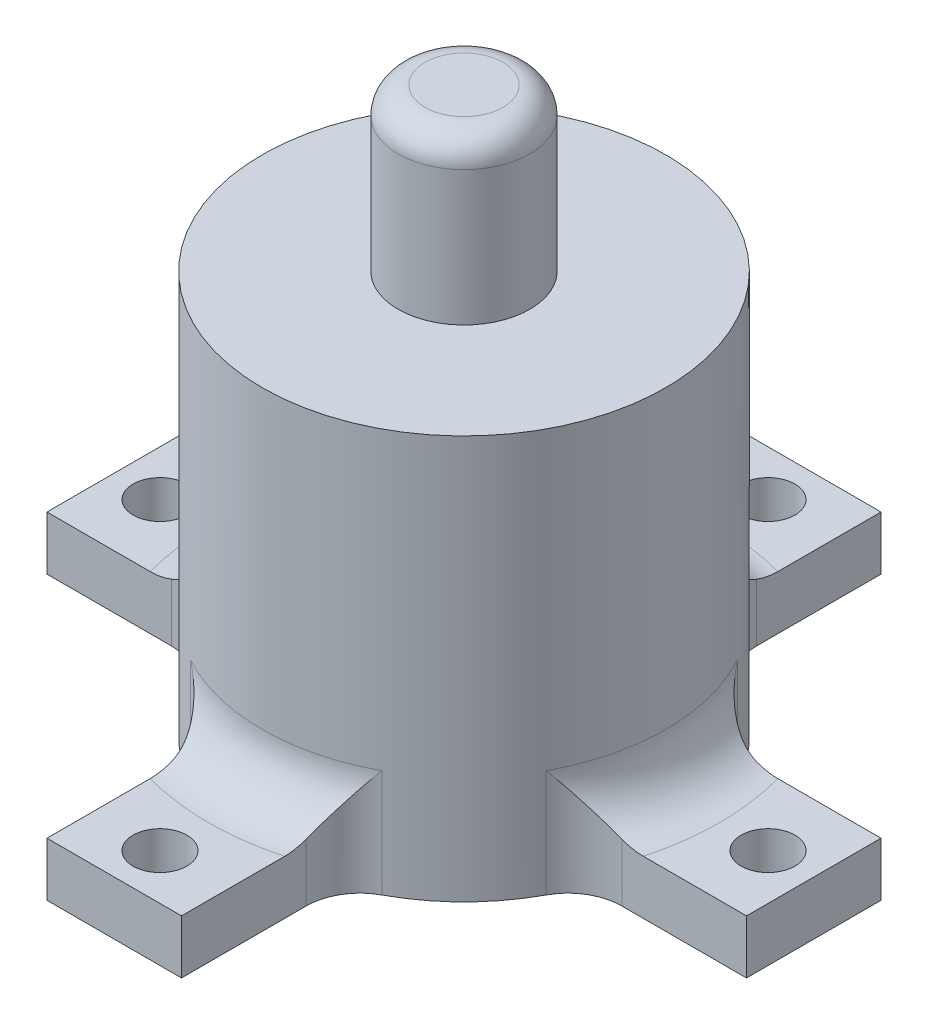
SolidWorks part; units mm, degrees
ref_plane "Front Plane" through (0, 0, 0) normal (0, 0, 1) x (1, 0, 0)
ref_plane "Top Plane" through (0, 0, 0) normal (0, 1, 0) x (1, 0, 0)
ref_plane "Right Plane" through (0, 0, 0) normal (1, 0, 0) x (0, 0, -1)
sketch "Sketch1" plane through (0, 0, 0) normal (0, 1, 0) x (1, 0, 0)
  circle A0 centre (0, 0) radius 7.5
  dimension "D1" = 15
extrude "Boss-Extrude1" add sketch "Sketch1" along normal blind 15
sketch "Sketch2" plane through (0, 15, 0) normal (0, 1, 0) x (1, 0, 0)
  circle A0 centre (0, 0) radius 2.45
  dimension "D1" = 4.9
extrude "Boss-Extrude2" add sketch "Sketch2" along normal blind 6
sketch "Sketch3" plane through (0, 0, 0) normal (0, 1, 0) x (1, 0, 0)
  line L1 (-2.5, 13) -> (2.5, 13)
  line L2 (-2.5, 13) -> (-2.5, -13)
  line L3 (-2.5, -13) -> (2.5, -13)
  line L4 (2.5, 13) -> (2.5, -13)
  line L5 (-13, 2.5) -> (13, 2.5)
  line L6 (-13, 2.5) -> (-13, -2.5)
  line L7 (-13, -2.5) -> (13, -2.5)
  line L8 (13, 2.5) -> (13, -2.5)
  circle A0 centre (0, 0) radius 7.5 construction
  circle A1 centre (0, 0) radius 7.5 construction
  point P10 (0, -13)
  point P14 (-13, 0)
  dimension "D3" = 13
  dimension "D1" = 5
  dimension "D2" = 13
  dimension "D4" = 5
  dimension "D5" = 26
  dimension "D6" = 13
extrude "Boss-Extrude3" add sketch "Sketch3" along normal blind 2 contours L6 L7 L2 L5 | L7 L2 L3 L4 | L8 L5 L4 L7 | L2 L5 L4 L1
fillet "Fillet1" radius 2 12 edges at (2.5, 1, 7.0711) (7.0711, 1, 2.5) (-2.5, 1, 7.0711) (-7.0711, 1, 2.5) (-7.0711, 1, -2.5) (-2.5, 1, -7.0711) (2.5, 1, -7.0711) (7.0711, 1, -2.5) (7.5, 2, 0) (0, 2, 7.5) (-7.5, 2, 0) (0, 2, -7.5)
hole_wizard "Ø2.0mm Dowel Hole1" positions "3DSketch1" profile "Sketch4" hole size "Ø2.0" standard "ANSI Metric" end condition through all
sketch3d "3DSketch1"
  line L0 (-13, 2, -2.5) -> (-13, 2, 2.5) construction
  line L1 (-2.5, 2, 13) -> (2.5, 2, 13) construction
  line L2 (13, 2, -2.5) -> (13, 2, 2.5) construction
  line L3 (-2.5, 2, -13) -> (2.5, 2, -13) construction
  line L4 (-13, 2, -2.5) -> (-9.1652, 2, -2.5) construction
  line L5 (-2.5, 2, -13) -> (-2.5, 2, -9.1652) construction
  line L6 (9.1652, 2, -2.5) -> (13, 2, -2.5) construction
  line L7 (-2.5, 2, 9.1652) -> (-2.5, 2, 13) construction
  point P0 (-11.3, 2, 0)
  point P2 (0, 2, -11.3)
  point P4 (11.3, 2, 0)
  point P6 (0, 2, 11.3)
  point P18 (0, 0, 0)
  dimension "D1" = 1.7
  dimension "D2" = 1.7
  dimension "D3" = 1.7
  dimension "D4" = 1.7
  dimension "D5" = 2.5
  dimension "D6" = 2.5
  dimension "D7" = 2.5
  dimension "D8" = 2.5
sketch "Sketch4" plane through (-11.3, 2, 0) normal (1, 0, 0) x (0, 0, 1)
  line L0 (0, 0) -> (0, 2)
  line L1 (0, 2) -> (1, 2)
  line L2 (1, 2) -> (1, 0)
  line L5 (1, 0) -> (0, 0)
  line L11 (0, -6.35) -> (0, 107.95) construction
  dimension "Thru Hole Dia." = 2
  dimension "Thru Hole Depth" = 2
fillet "Fillet2" radius 1 1 edges at (0, 21, 2.45)
